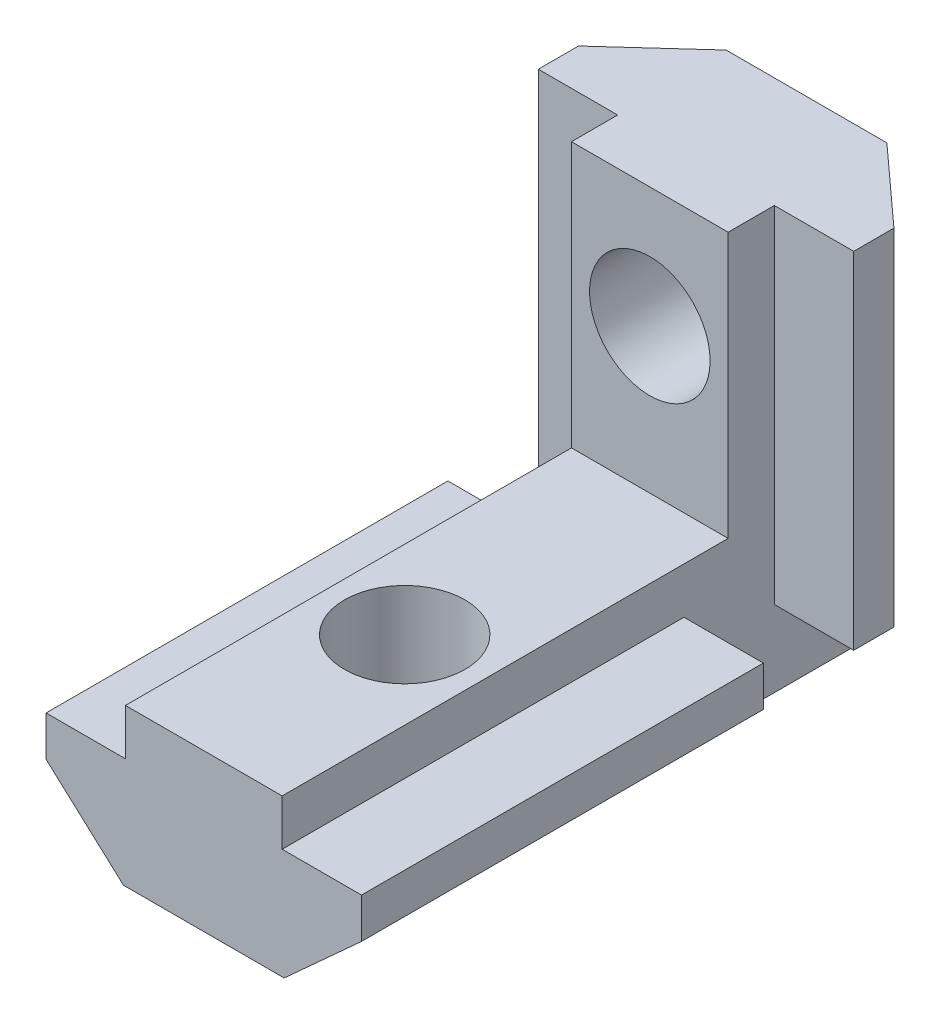
SolidWorks part; units mm, degrees
material "Оцинкованная сталь"
ref_plane "Спереди" through (0, 0, 0) normal (0, 0, 1) x (1, 0, 0)
ref_plane "Сверху" through (0, 0, 0) normal (0, 1, 0) x (1, 0, 0)
ref_plane "Справа" through (0, 0, 0) normal (1, 0, 0) x (0, 0, -1)
sketch "Эскиз1" plane through (0, 0, 0) normal (0, 0, 1) x (1, 0, 0)
  line L0 (3.9, -2.3) -> (-3.9, -2.3) construction
  line L1 (-3.9, -2.3) -> (-3.9, 0) construction
  line L2 (-3.9, 0) -> (-7.85, 0) construction
  line L3 (-7.85, 0) -> (-7.85, 2) construction
  line L4 (0, 10.717) -> (0, -7.7878) construction
  line L5 (-7.85, 2) -> (-4, 5.5) construction
  line L6 (-4, 5.5) -> (4, 5.5) construction
  line L7 (3.9, -2.3) -> (3.9, 0) construction
  line L8 (3.9, 0) -> (7.85, 0) construction
  line L9 (7.85, 0) -> (7.85, 2) construction
  line L10 (7.85, 2) -> (4, 5.5) construction
  line L11 (-18.6564, 1.6) -> (16.3912, 1.6) construction
  line L12 (-3.9, 8.3153) -> (3.9, 8.3153)
  line L13 (3.9, 8.3153) -> (3.9, 3.2)
  line L14 (3.9, 3.2) -> (7.85, 3.2)
  line L15 (7.85, 3.2) -> (7.85, 1.2)
  line L16 (7.85, 1.2) -> (4, -2.3)
  line L17 (4, -2.3) -> (-4, -2.3)
  line L18 (-3.9, 8.3153) -> (-3.9, 3.2)
  line L19 (-3.9, 3.2) -> (-7.85, 3.2)
  line L20 (-7.85, 3.2) -> (-7.85, 1.2)
  line L21 (-7.85, 1.2) -> (-4, -2.3)
  point P11 (0, -2.3)
  point P15 (0, 5.5)
  point P24 (0, 8.3153)
  point P28 (0, -2.3)
  dimension "D1" = 3.9
  dimension "D2" = 2.3
  dimension "D3" = 3.95
  dimension "D4" = 5.5
  dimension "D5" = 4
  dimension "D6" = 7.8
  dimension "D7" = 2
  dimension "D8" = 15.7
  dimension "D9" = 3.9
extrude "Бобышка-Вытянуть1" add sketch "Эскиз1" along normal blind 20 and the other way blind 0.0001
sketch "Эскиз2" plane through (0, 0, -0.0001) normal (0, 0, -1) x (-1, 0, 0)
  line L0 (-3.9, -2.3) -> (-3.9, 5.5)
  line L2 (-3.9, 5.5) -> (3.9, 5.5)
  line L3 (3.9, 5.5) -> (3.9, -2.3)
  line L4 (3.9, -2.3) -> (-3.9, -2.3)
extrude "Бобышка-Вытянуть2" add sketch "Эскиз2" along normal blind 10
ref_plane "Плоскость1" through (0, 5.5, 0) normal (0, 1, 0) x (1, 0, 0)
sketch "Эскиз3" plane through (0, 5.5, 0) normal (0, 1, 0) x (1, 0, 0)
  line L0 (3.9, 2.2001) -> (-3.9, 2.2001)
  line L1 (-3.9, 2.2001) -> (-3.9, 4.5001)
  line L2 (-3.9, 4.5001) -> (-7.85, 4.5001)
  line L3 (-7.85, 4.5001) -> (-7.85, 6.5001)
  line L4 (0, 9.5043) -> (0, -2.2459) construction
  line L5 (-7.85, 6.5001) -> (-4, 10.0001)
  line L6 (-4, 10.0001) -> (4, 10.0001)
  line L7 (3.9, 2.2001) -> (3.9, 4.5001)
  line L8 (3.9, 4.5001) -> (7.85, 4.5001)
  line L9 (7.85, 4.5001) -> (7.85, 6.5001)
  line L10 (7.85, 6.5001) -> (4, 10.0001)
  line L11 (0, 10.0001) -> (0, -22.2262) construction
  line L12 (-3.9, 10.0001) -> (3.9, 10.0001) construction
  point P9 (0, 2.2001)
  point P13 (0, 10.0001)
  dimension "D1" = 3.9
  dimension "D2" = 2.3
  dimension "D3" = 3.95
  dimension "D4" = 5.5
  dimension "D5" = 4
  dimension "D6" = 7.8
  dimension "D7" = 2
extrude "Бобышка-Вытянуть3" add sketch "Эскиз3" along normal blind 13.2 and the other way blind 4
sketch "Эскиз4" plane through (0, 8.3153, 0) normal (0, 1, 0) x (1, 0, 0)
  line L1 (-3.9, -20) -> (-7.85, -20) construction
  circle A0 centre (0, -10) radius 3
  dimension "D1" = 10
extrude "Вырез-Вытянуть1" cut sketch "Эскиз4" against normal through all
cosmetic thread "Условное изображение резьбы1" parameters "D2"=8
sketch "Эскиз5" plane through (0, 0, -2.2001) normal (0, 0, 1) x (1, 0, 0)
  line L0 (-3.9, 18.7) -> (3.9, 18.7) construction
  circle A0 centre (0, 12.7) radius 3
  dimension "D1" = 6
extrude "Вырез-Вытянуть2" cut sketch "Эскиз5" against normal through all
cosmetic thread "Условное изображение резьбы2" parameters "D2"=8
sketch "Эскиз6" plane through (0, 0, -0.0001) normal (0, 0, -1) x (-1, 0, 0)
  line L1 (3.9, 8.3153) -> (-3.9, 8.3153)
  line L2 (3.9, 8.3153) -> (3.9, 5.5)
  line L3 (3.9, 5.5) -> (-3.9, 5.5)
  line L4 (-3.9, 8.3153) -> (-3.9, 5.5)
extrude "Вырез-Вытянуть3" cut sketch "Эскиз6" against normal through all
